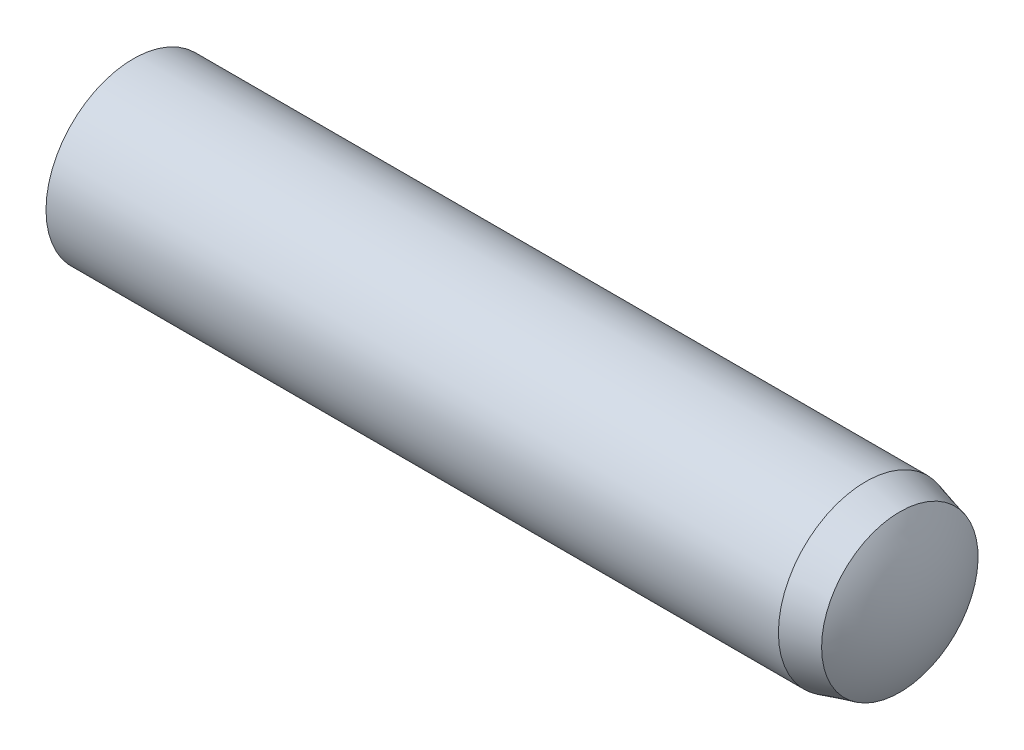
SolidWorks part; units mm, degrees
material "1023 Carbon Steel Sheet (SS)"
ref_plane "Front Plane" through (0, 0, 0) normal (0, 0, 1) x (1, 0, 0)
ref_plane "Top Plane" through (0, 0, 0) normal (0, 1, 0) x (1, 0, 0)
ref_plane "Right Plane" through (0, 0, 0) normal (1, 0, 0) x (0, 0, -1)
sketch "Sketch1" plane through (0, 0, 0) normal (0, 0, 1) x (1, 0, 0)
  line L0 (-7, 0) -> (7, 0) construction
  line L1 (7, 1.5) -> (7, -1.5) construction
  line L2 (-7, 1.5) -> (-7, -1.5) construction
  line L3 (6.025, 1.5) -> (6.025, -1.5) construction
  line L4 (-6.55, 1.5) -> (-6.55, -1.5) construction
  line L5 (-7, 0) -> (-6.55, 0) construction
  line L6 (7, 0) -> (6.025, 0) construction
  line L7 (6.61, 1.5) -> (6.61, -1.5) construction
  dimension "Dia" = 3
  dimension "Length" = 14
  dimension "D1" = 0.975
  dimension "D2" = 0.45
  dimension "D3" = 0.585
sketch "Sketch2" plane through (0, 0, 0) normal (1, 0, 0) x (0, 0, -1)
  circle A0 centre (0, 0) radius 1.5
extrude "Extrude1" add sketch "Sketch2" against normal up to vertex (7 mm away) and the other way up to vertex (7 mm away) up to point (-7, 0, 0) other way up to point (7, 0, 0)
sketch "Sketch5" plane through (0, 0, 0) normal (0, 0, 1) x (1, 0, 0)
  line L0 (6.025, 1.5) -> (6.025, 2)
  line L1 (6.025, 2) -> (7.5, 2)
  line L2 (7.5, 2) -> (7.5, 0)
  line L3 (7, 0) -> (7.5, 0)
  line L5 (-6.55, 1.5) -> (-6.55, 2)
  line L6 (-6.55, 2) -> (-7.5, 2)
  line L7 (-7.5, 2) -> (-7.5, 0)
  line L8 (6.025, 1.5) -> (6.61, 1.3432)
  line L10 (-7, 0) -> (-7.5, 0)
  line L11 (-7, 1.5) -> (-7, -1.5) construction
  line L13 (6.025, 1.5) -> (6.025, -1.5) construction
  line L15 (-7, 0) -> (7, 0) construction
  line L16 (6.61, 1.5) -> (6.61, -1.5) construction
  line L17 (7, 1.5) -> (7, -1.5) construction
  arc A0 (6.61, 1.3432) -> (7, 0) centre (4.4918, 0) cw
  arc A1 (-6.55, 1.5) -> (-7, 0) centre (-4.275, 0) ccw
  dimension "D1" = 15
  dimension "D2" = 0.5
revolve "Cut-Revolve1" cut sketch "Sketch5" angle 360 about L0
equation "\"D1@Sketch1\" = \"Dia@Sketch1\"*.325"
equation "\"D2@Sketch1\" = \"Dia@Sketch1\"*.15"
equation "\"D3@Sketch1\" = \"D1@Sketch1\"*.6"
